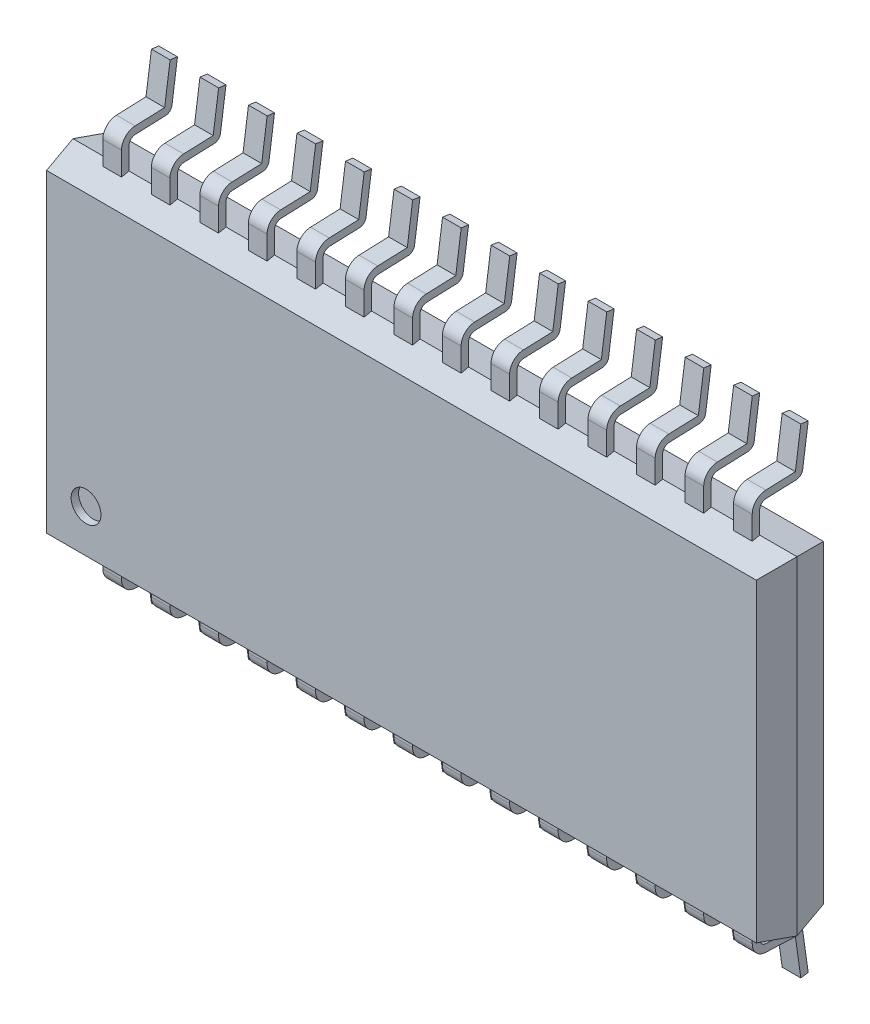
SolidWorks part; units mm, degrees
ref_plane "Front Plane" through (0, 0, 0) normal (0, 0, 1) x (1, 0, 0)
ref_plane "Top Plane" through (0, 0, 0) normal (0, 1, 0) x (1, 0, 0)
ref_plane "Right Plane" through (0, 0, 0) normal (1, 0, 0) x (0, 0, -1)
sketch "Sketch1" plane through (0, 0, 0) normal (0, 0, 1) x (1, 0, 0)
  line L1 (0, 0) -> (9.7, 0)
  line L2 (0, 0) -> (0, 4.4)
  line L3 (0, 4.4) -> (9.7, 4.4)
  line L4 (9.7, 0) -> (9.7, 4.4)
  dimension "D1" = 4.4
  dimension "D2" = 9.7
extrude "Boss-Extrude1" add sketch "Sketch1" along normal blind 0.45 draft 12
sketch "Sketch2" plane through (0, 0, 0) normal (0, 0, -1) x (-1, 0, 0)
  line L1 (-9.7, 4.4) -> (0, 4.4)
  line L2 (-9.7, 4.4) -> (-9.7, 0)
  line L3 (-9.7, 0) -> (0, 0)
  line L4 (0, 4.4) -> (0, 0)
extrude "Boss-Extrude2" add sketch "Sketch2" along normal blind 0.45 draft 12
ref_plane "Plane1" through (0.625, 0, 0) normal (1, 0, 0) x (0, 0, -1)
sketch "Sketch3" plane through (0.625, 0, 0) normal (1, 0, 0) x (0, 0, -1)
  line L0 (0, 0.0306) -> (0, -0.2918)
  line L1 (0, 0) -> (0, 4.4) construction
  line L2 (0.0866, -0.3817) -> (0.4905, -0.3971)
  line L3 (0.5762, -0.4745) -> (0.65, -1)
  line L4 (0.45, 4.3043) -> (0.45, 0.0957) construction
  line L5 (-0.45, 0.0957) -> (-0.45, 4.3043) construction
  arc A0 (0.0866, -0.3817) -> (0, -0.2918) centre (0.09, -0.2918) cw
  arc A1 (0.5762, -0.4745) -> (0.4905, -0.3971) centre (0.487, -0.4871) ccw
  point P16 (0.5657, -0.4)
  dimension "D5" = 0.09
  dimension "D6" = 0.09
  dimension "D1" = 0.6
  dimension "D2" = 1
  dimension "D3" = 8
  dimension "D4" = 1.1
extrude "Extrude-Thin1" add sketch "Sketch3" along normal mid plane 0.25 thin
pattern_linear "LPattern1" count 14 spacing 0.65 along (1, 0, 0) of "Extrude-Thin1"
ref_plane "Plane2" through (0, 2.2, 0) normal (0, 1, 0) x (1, 0, 0)
mirror "Mirror1" about plane through (0, 2.2, 0) normal (0, 1, 0) of "LPattern1", "Extrude-Thin1"
sketch "Sketch4" plane through (0, 0, 0.45) normal (0, 0, 1) x (1, 0, 0)
  line L0 (0.625, -0.605) -> (0.625, 0.605) construction
  circle A0 centre (0.625, 0.6713) radius 0.2
  dimension "D1" = 0.4
extrude "Cut-Extrude1" cut sketch "Sketch4" against normal blind 0.1
